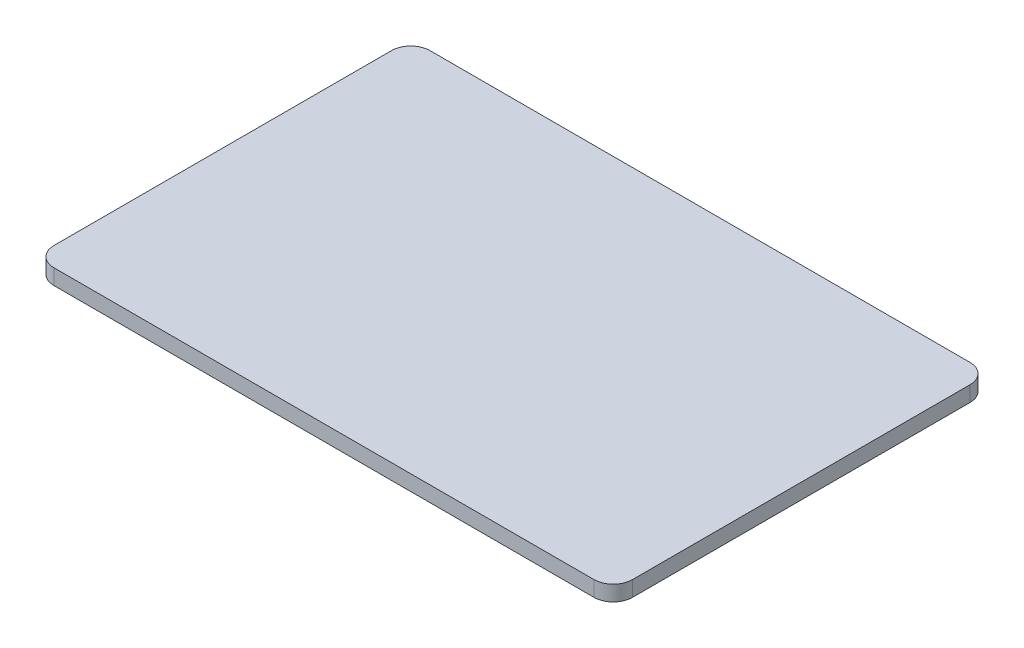
SolidWorks part; units mm, degrees
ref_plane "Front Plane" through (0, 0, 0) normal (0, 0, 1) x (1, 0, 0)
ref_plane "Top Plane" through (0, 0, 0) normal (0, 1, 0) x (1, 0, 0)
ref_plane "Right Plane" through (0, 0, 0) normal (1, 0, 0) x (0, 0, -1)
sketch "Sketch1" plane through (0, 0, 0) normal (0, 1, 0) x (1, 0, 0)
  line L1 (20, -19.5) -> (-20, -19.5)
  line L2 (20, -19.5) -> (20, 19.5)
  line L3 (20, 19.5) -> (-20, 19.5)
  line L4 (-20, -19.5) -> (-20, 19.5)
  line L5 (20, -19.5) -> (-20, 19.5) construction
  line L6 (20, 19.5) -> (-20, -19.5) construction
  point P0 (0, 0)
  dimension "D1" = 40
  dimension "D2" = 39
extrude "Boss-Extrude1" add sketch "Sketch1" along normal blind 1.6
sketch "Sketch2" plane through (0, 0, 0) normal (0, 1, 0) x (1, 0, 0)
  line L1 (-20, 19.5) -> (-40, 19.5)
  line L2 (-20, 19.5) -> (-20, -19.5)
  line L3 (-20, -19.5) -> (-40, -19.5)
  line L4 (-40, 19.5) -> (-40, -19.5)
  dimension "D1" = 20
extrude "Boss-Extrude2" add sketch "Sketch2" along normal up to surface (1.6 mm away) up to face at (0, 1.6, 0)
fillet "Fillet1" radius 2 4 edges at (20, 0.8, -19.5) (20, 0.8, 19.5) (-40, 0.8, -19.5) (-40, 0.8, 19.5)
